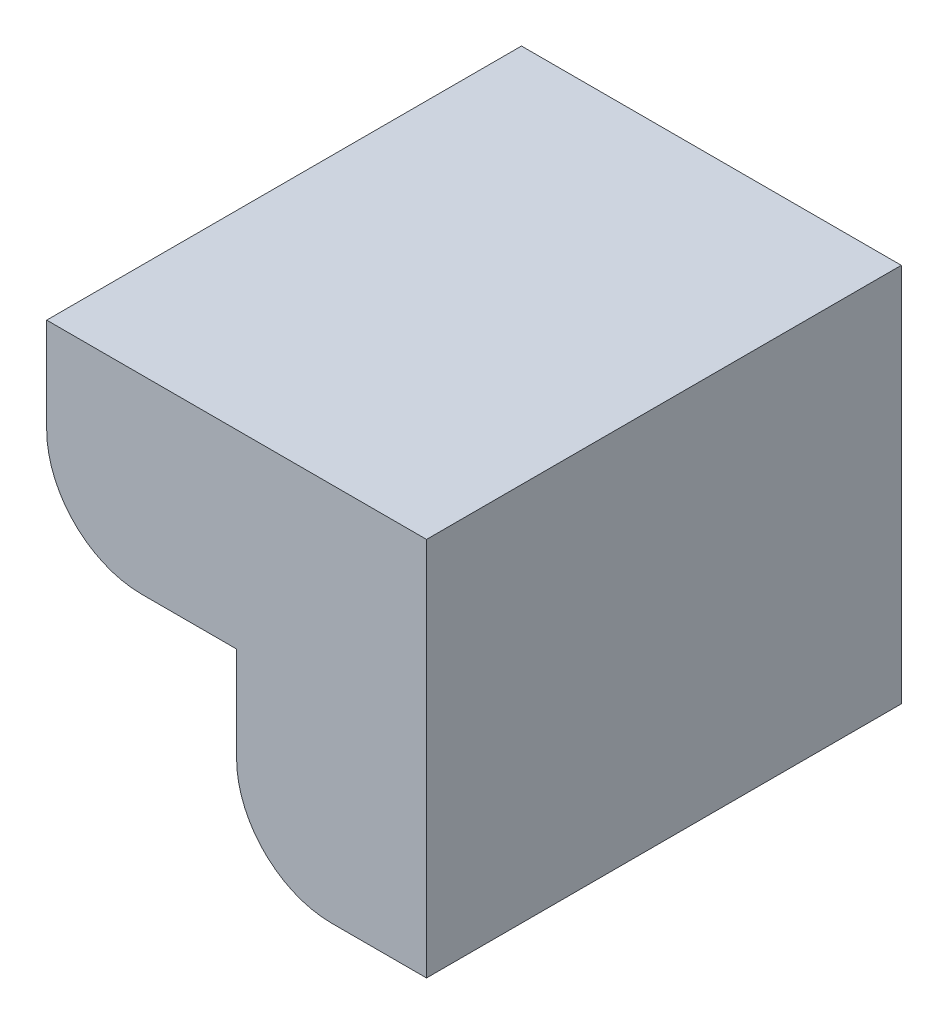
SolidWorks part; units mm, degrees
ref_plane "Front Plane" through (0, 0, 0) normal (0, 0, 1) x (1, 0, 0)
ref_plane "Top Plane" through (0, 0, 0) normal (0, 1, 0) x (1, 0, 0)
ref_plane "Right Plane" through (0, 0, 0) normal (1, 0, 0) x (0, 0, -1)
sketch "Sketch1" plane through (0, 0, 0) normal (0, 0, 1) x (1, 0, 0)
  line L0 (-10, 10) -> (10, 10)
  line L1 (10, 10) -> (10, -10)
  line L2 (10, -10) -> (5, -10)
  line L3 (0, -5) -> (0, 0)
  line L4 (0, 0) -> (-5, 0)
  line L5 (-10, 10) -> (-10, 5)
  arc A0 (5, -10) -> (0, -5) centre (5, -5) cw
  arc A1 (-5, 0) -> (-10, 5) centre (-5, 5) cw
  dimension "D6" = 5
  dimension "D1" = 20
  dimension "D2" = 20
  dimension "D3" = 5
  dimension "D4" = 5
  dimension "D5" = 5
extrude "Boss-Extrude1" add sketch "Sketch1" along normal blind 25
